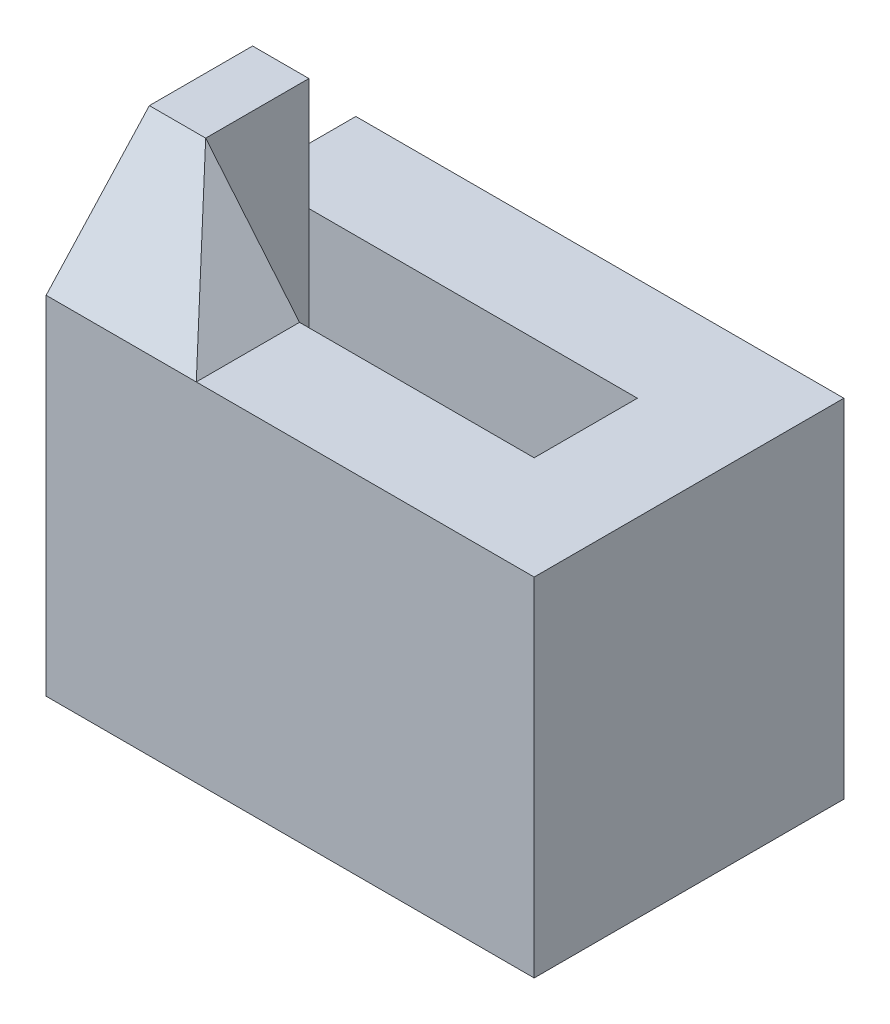
SolidWorks part; units mm, degrees
material "灰铸铁"
ref_plane "前视基准面" through (0, 0, 0) normal (0, 0, 1) x (1, 0, 0)
ref_plane "上视基准面" through (0, 0, 0) normal (0, 1, 0) x (1, 0, 0)
ref_plane "右视基准面" through (0, 0, 0) normal (1, 0, 0) x (0, 0, -1)
sketch "草图1" plane through (0, 0, 0) normal (0, 1, 0) x (1, 0, 0)
  line L0 (-32.9695, 0) -> (85.0664, 0) construction
  line L1 (-26, 16.5) -> (26, 16.5)
  line L2 (-26, 16.5) -> (-26, -16.5)
  line L3 (-26, -16.5) -> (26, -16.5)
  line L4 (26, 16.5) -> (26, -16.5)
  line L5 (0, -46.4342) -> (0, 59.2696) construction
  line L7 (-20, 5.5) -> (2, 5.5)
  line L8 (-20, 5.5) -> (-20, -5.5)
  line L9 (-20, -5.5) -> (2, -5.5)
  line L10 (2, 5.5) -> (2, -5.5)
  dimension "D1" = 33
  dimension "D2" = 52
  dimension "D3" = 6
  dimension "D4" = 22
  dimension "D5" = 11
extrude "凸台-拉伸1" add sketch "草图1" along normal blind 37
sketch "草图3" plane through (0, 37, 0) normal (0, 1, 0) x (1, 0, 0)
  line L1 (2, 5.5) -> (15, 5.5)
  line L2 (2, 5.5) -> (2, -5.5)
  line L3 (2, -5.5) -> (15, -5.5)
  line L4 (15, 5.5) -> (15, -5.5)
  dimension "D1" = 11
  dimension "D2" = 13
extrude "切除-拉伸1" cut sketch "草图3" against normal blind 13
sketch "草图4" plane through (0, 37, 0) normal (0, 1, 0) x (1, 0, 0)
  line L0 (-26, 16.5) -> (-26, -16.5) construction
  line L1 (-20, 5.5) -> (-26, 5.5)
  line L2 (-20, 5.5) -> (-20, -5.5)
  line L3 (-20, -5.5) -> (-26, -5.5)
  line L4 (-26, 5.5) -> (-26, -5.5)
  dimension "D1" = 11
extrude "凸台-拉伸2" add sketch "草图4" along normal blind 12
sketch "草图5" plane through (0, 37, 0) normal (0, 1, 0) x (1, 0, 0)
  line L0 (-26, -16.5) -> (26, -16.5) construction
  line L1 (-26, -5.5) -> (-10, -5.5)
  line L2 (-26, -5.5) -> (-26, -16.5)
  line L3 (-26, -16.5) -> (-10, -16.5)
  line L4 (-10, -5.5) -> (-10, -16.5)
  dimension "D1" = 16
sketch "草图6" plane through (-26, 0, 0) normal (-1, 0, 0) x (0, 0, 1)
  line L0 (5.5, 49) -> (16.5, 37)
  line L1 (16.5, 37) -> (5.5, 37)
  line L2 (5.5, 37) -> (5.5, 49)
extrude "凸台-拉伸4" add sketch "草图6" against normal up to vertex (16 mm away) up to point (-10, 37, 16.5)
sketch "草图7" plane through (0, 0, 16.5) normal (0, 0, 1) x (1, 0, 0)
  line L0 (-20, 49) -> (-10, 37)
  line L1 (-10, 37) -> (-10, 49)
  line L2 (-10, 49) -> (-20, 49)
extrude "切除-拉伸2" cut sketch "草图7" against normal up to next
